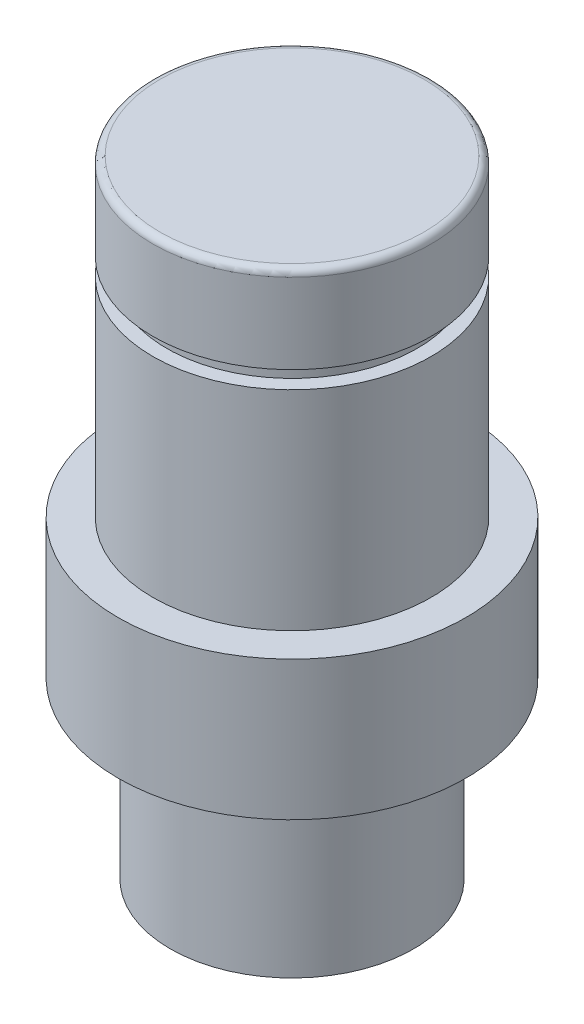
SolidWorks part; units mm, degrees
material "Nylon 101"
ref_plane "Front Plane" through (0, 0, 0) normal (0, 0, 1) x (1, 0, 0)
ref_plane "Top Plane" through (0, 0, 0) normal (0, 1, 0) x (1, 0, 0)
ref_plane "Right Plane" through (0, 0, 0) normal (1, 0, 0) x (0, 0, -1)
sketch "Sketch2" plane through (0, 0, 0) normal (0, 0, 1) x (1, 0, 0)
  line L2 (-3.9452, 11.1954) -> (-3.9452, 8.6954)
  line L3 (-3.9452, 2.1954) -> (-4.9452, 2.1954)
  line L4 (-4.9452, 2.1954) -> (-4.9452, -1.8046)
  line L5 (-4.9452, -1.8046) -> (-3.4452, -1.8046)
  line L6 (-3.4452, -1.8046) -> (-3.4452, -6.8046)
  line L7 (-3.4452, -6.8046) -> (0.0548, -6.8046)
  line L8 (0.0548, -6.8046) -> (0.0548, 11.1954) construction
  line L10 (0.0548, -6.8046) -> (0.0548, 11.1954)
  line L11 (-3.9452, 8.1954) -> (-3.5452, 8.1954)
  line L12 (-3.5452, 8.1954) -> (-3.5452, 8.6954)
  line L13 (-3.5452, 8.6954) -> (-3.9452, 8.6954)
  line L14 (-3.9452, 8.1954) -> (-3.9452, 2.1954)
  line L15 (-3.9452, 11.1954) -> (0.0548, 11.1954)
  dimension "D1" = 4
  dimension "D2" = 3.5
  dimension "D3" = 5
  dimension "D4" = 4
  dimension "D5" = 5
  dimension "D6" = 18
  dimension "D9" = 0.4
  dimension "D10" = 0.5
  dimension "D11" = 6
revolve "Revolve1" add sketch "Sketch2" angle 360 about L8
fillet "Fillet1" radius 0.2 1 edges at (0.0548, 11.1954, -4)
